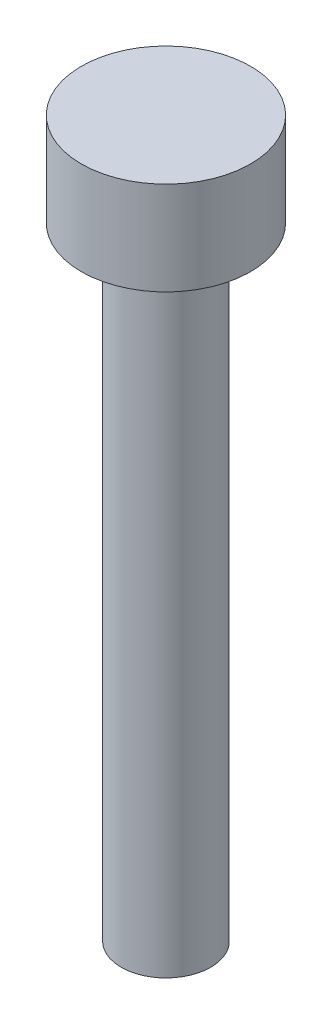
SolidWorks part; units mm, degrees
ref_plane "Front Plane" through (0, 0, 0) normal (0, 0, 1) x (1, 0, 0)
ref_plane "Top Plane" through (0, 0, 0) normal (0, 1, 0) x (1, 0, 0)
ref_plane "Right Plane" through (0, 0, 0) normal (1, 0, 0) x (0, 0, -1)
sketch "Sketch1" plane through (0, 0, 0) normal (0, 1, 0) x (1, 0, 0)
  circle A0 centre (0, 0) radius 2.72
  dimension "D1" = 5.44
extrude "Boss-Extrude1" add sketch "Sketch1" along normal blind 3
sketch "Sketch2" plane through (0, 0, 0) normal (0, -1, 0) x (1, 0, 0)
  circle A0 centre (0, 0) radius 1.44
  dimension "D1" = 2.88
extrude "Boss-Extrude2" add sketch "Sketch2" along normal blind 20
